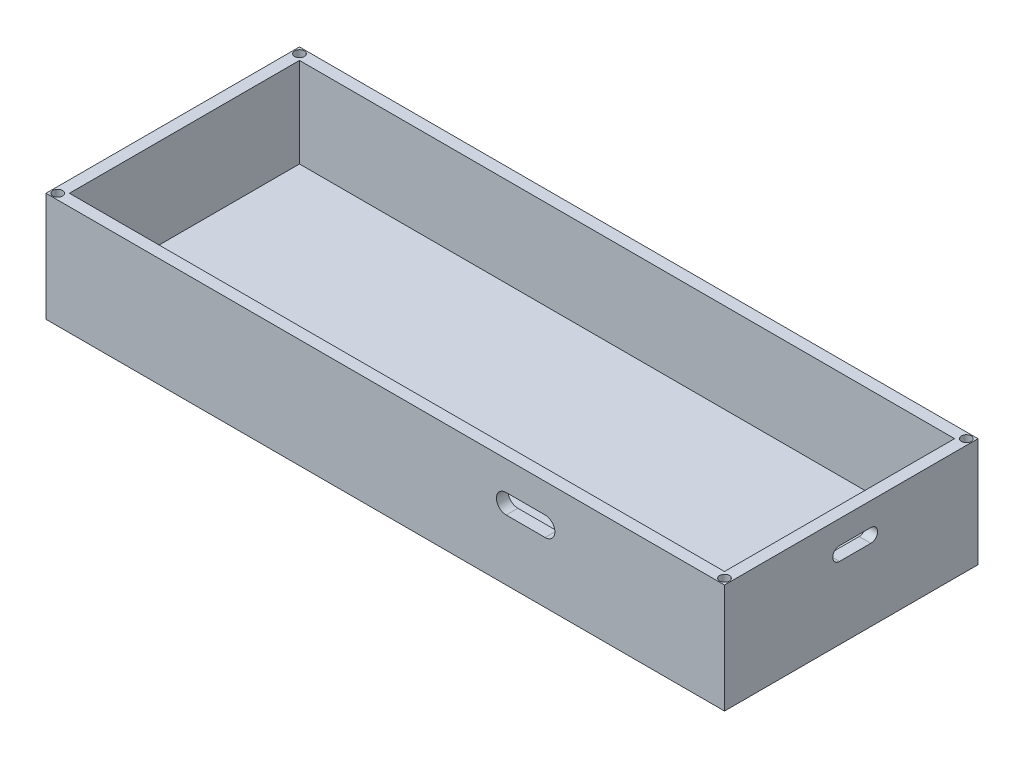
SolidWorks part; units mm, degrees
ref_plane "Front Plane" through (0, 0, 0) normal (0, 0, 1) x (1, 0, 0)
ref_plane "Top Plane" through (0, 0, 0) normal (0, 1, 0) x (1, 0, 0)
ref_plane "Right Plane" through (0, 0, 0) normal (1, 0, 0) x (0, 0, -1)
sketch "Sketch1" plane through (0, 0, 0) normal (0, 1, 0) x (1, 0, 0)
  line L1 (0, 0) -> (174, 0)
  line L2 (0, 0) -> (0, 65)
  line L3 (0, 65) -> (174, 65)
  line L4 (174, 0) -> (174, 65)
  dimension "D1" = 65
  dimension "D2" = 174
extrude "Boss-Extrude1" add sketch "Sketch1" along normal blind 5
sketch "Sketch2" plane through (0, 5, 0) normal (0, 1, 0) x (1, 0, 0)
  line L0 (174, 0) -> (174, 65) construction
  line L1 (0, 65) -> (174, 65)
  line L2 (0, 65) -> (0, 0)
  line L3 (0, 0) -> (174, 0)
  line L4 (174, 65) -> (174, 0)
  line L5 (0, 0) -> (174, 0) construction
  line L6 (3, 62) -> (3, 3)
  line L7 (3, 3) -> (171, 3)
  line L8 (171, 62) -> (171, 3)
  line L9 (3, 62) -> (171, 62)
  dimension "D1" = 3
extrude "Boss-Extrude2" add sketch "Sketch2" along normal blind 23
sketch "Sketch3" plane through (174, 0, 0) normal (1, 0, 0) x (0, 0, -1)
  line L0 (29.5, 20.25) -> (37.5, 20.25) construction
  line L1 (29.5, 22) -> (37.5, 22)
  line L2 (29.5, 18.5) -> (37.5, 18.5)
  line L3 (0, 28) -> (0, 0) construction
  line L4 (0, 0) -> (65, 0) construction
  arc A0 (29.5, 22) -> (29.5, 18.5) centre (29.5, 20.25) ccw
  arc A1 (37.5, 18.5) -> (37.5, 22) centre (37.5, 20.25) ccw
  point P2 (33.5, 20.25)
  dimension "D1" = 8
  dimension "D2" = 3.5
  dimension "D3" = 29.5
  dimension "D4" = 18.5
extrude "Cut-Extrude2" cut sketch "Sketch3" against normal blind 23
sketch "Sketch4" plane through (0, 28, 0) normal (0, 1, 0) x (1, 0, 0)
  line L0 (3, 3) -> (0, 0) construction
  circle A0 centre (1.5, 1.5) radius 1.25
  dimension "D1" = 2.5
extrude "Cut-Extrude3" cut sketch "Sketch4" against normal blind 4
pattern_linear "LPattern2" count 2 spacing 62 along (0, 0, -1) count 2 spacing 171 along (1, 0, 0) of "Cut-Extrude3"
sketch "Sketch5" plane through (0, 0, 0) normal (0, 0, 1) x (1, 0, 0)
  line L0 (174, 14) -> (128, 14) construction
  line L1 (174, 28) -> (174, 0) construction
  line L2 (128, 0) -> (128, 18.05) construction
  line L3 (0, 0) -> (174, 0) construction
  line L4 (128, 18.05) -> (118, 18.05) construction
  line L5 (128, 15.55) -> (118, 15.55)
  line L6 (128, 20.55) -> (118, 20.55)
  arc A0 (128, 15.55) -> (128, 20.55) centre (128, 18.05) ccw
  arc A1 (118, 20.55) -> (118, 15.55) centre (118, 18.05) ccw
  point P8 (123, 18.05)
  dimension "D1" = 46
  dimension "D2" = 18.05
  dimension "D3" = 10
  dimension "D4" = 5
extrude "Cut-Extrude4" cut sketch "Sketch5" against normal blind 10
